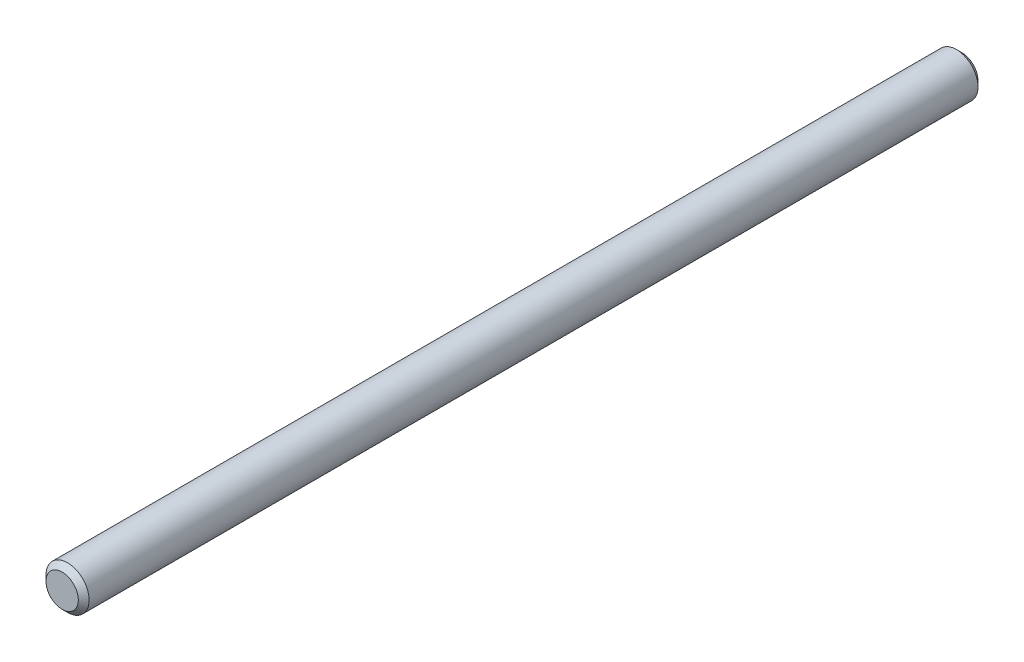
SolidWorks part; units mm, degrees
ref_plane "Piano frontale" through (0, 0, 0) normal (0, 0, 1) x (1, 0, 0)
ref_plane "Piano superiore" through (0, 0, 0) normal (0, 1, 0) x (1, 0, 0)
ref_plane "Piano destro" through (0, 0, 0) normal (1, 0, 0) x (0, 0, -1)
ref_plane "Plane1" through (0, 0, 64.8812) normal (0, 0, -1) x (-1, 0, 0)
sketch "Schizzo1" plane through (0, 0, 64.8812) normal (0, 0, 1) x (1, 0, 0)
  circle A0 centre (0, 0) radius 4
  dimension "D1" = 8
extrude "Estrusione-Estrusione1" add sketch "Schizzo1" along normal up to surface (167 mm away)
chamfer "Smusso1" distance 1 angle 45 2 edges at (0, -4, 231.8812) (4, 0, 64.8812)
